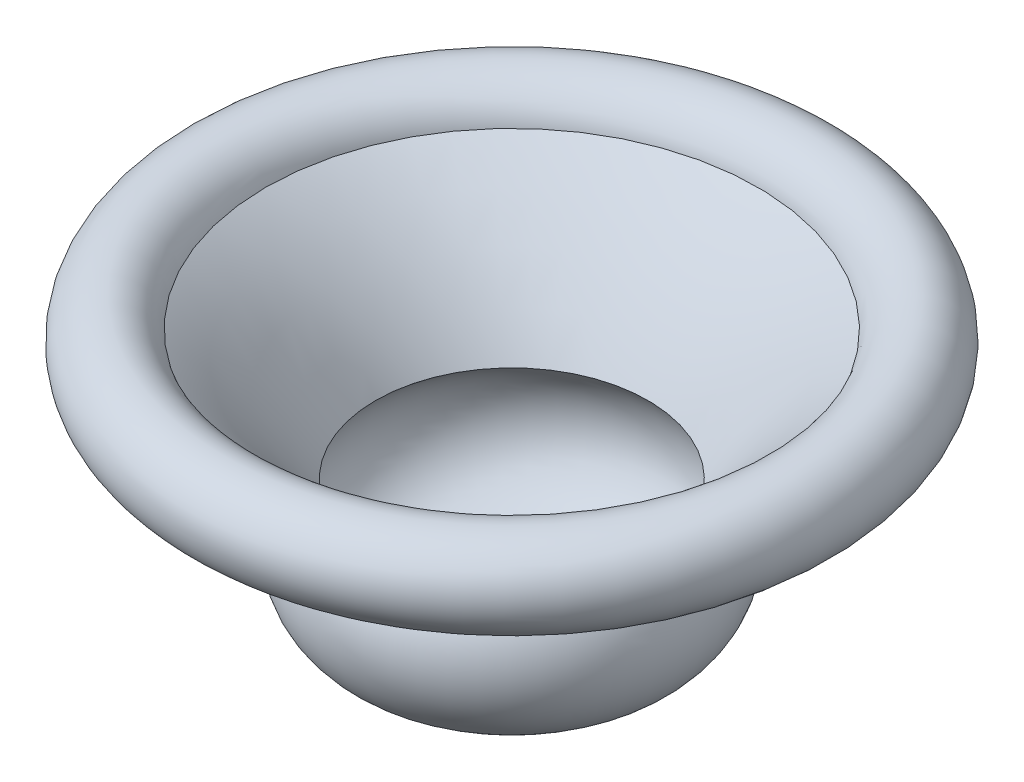
SolidWorks part; units mm, degrees
ref_plane "Front Plane" through (0, 0, 0) normal (0, 0, 1) x (1, 0, 0)
ref_plane "Top Plane" through (0, 0, 0) normal (0, 1, 0) x (1, 0, 0)
ref_plane "Right Plane" through (0, 0, 0) normal (1, 0, 0) x (0, 0, -1)
sketch "Sketch1" plane through (0, 0, 0) normal (0, 0, 1) x (1, 0, 0)
  line L0 (0, 0) -> (0, -71.8384) construction
  line L1 (0, 0) -> (168.5918, 0) construction
  line L2 (108.1425, 68.3038) -> (105.4357, 72.5078)
  line L3 (26.7691, -7.2689) -> (19.1465, -7.2689)
  line L5 (27.9602, -2.4129) -> (19.1465, -2.2689)
  line L7 (0, 3.9332) -> (0, 8.9334)
  arc A0 (26.7691, -7.2689) -> (53.7866, 40.2798) centre (33.5396, 20.3341) ccw
  arc A1 (53.7866, 40.2798) -> (90.3052, 81.6239) centre (172.6433, -27.9041) cw
  arc A2 (90.3052, 81.6239) -> (105.4357, 72.5078) centre (100.1088, 80.781) cw
  arc A3 (27.9602, -2.4129) -> (47.4559, 39.1728) centre (33.5396, 20.3341) ccw
  arc A4 (47.4559, 39.1728) -> (85.721, 84.4156) centre (172.6433, -27.9041) cw
  arc A5 (85.721, 84.4156) -> (108.1425, 68.3038) centre (100.1088, 80.781) cw
  arc A6 (10.3998, -2.1161) -> (0, 3.9332) centre (0.13, -7.8074) ccw
  arc A7 (19.1465, -7.2689) -> (10.3998, -2.1161) centre (19.1465, 2.7311) cw
  arc A14 (19.1465, -2.2689) -> (14.7731, 0.3075) centre (19.1465, 2.7311) cw
  arc A15 (14.7731, 0.3075) -> (0, 8.9334) centre (0.13, -7.8074) ccw
  point P24 (27.5201, -2.4129)
  dimension "D1" = 5
  dimension "D2" = 10
revolve "Revolve3" add sketch "Sketch1" angle 360 about L0
